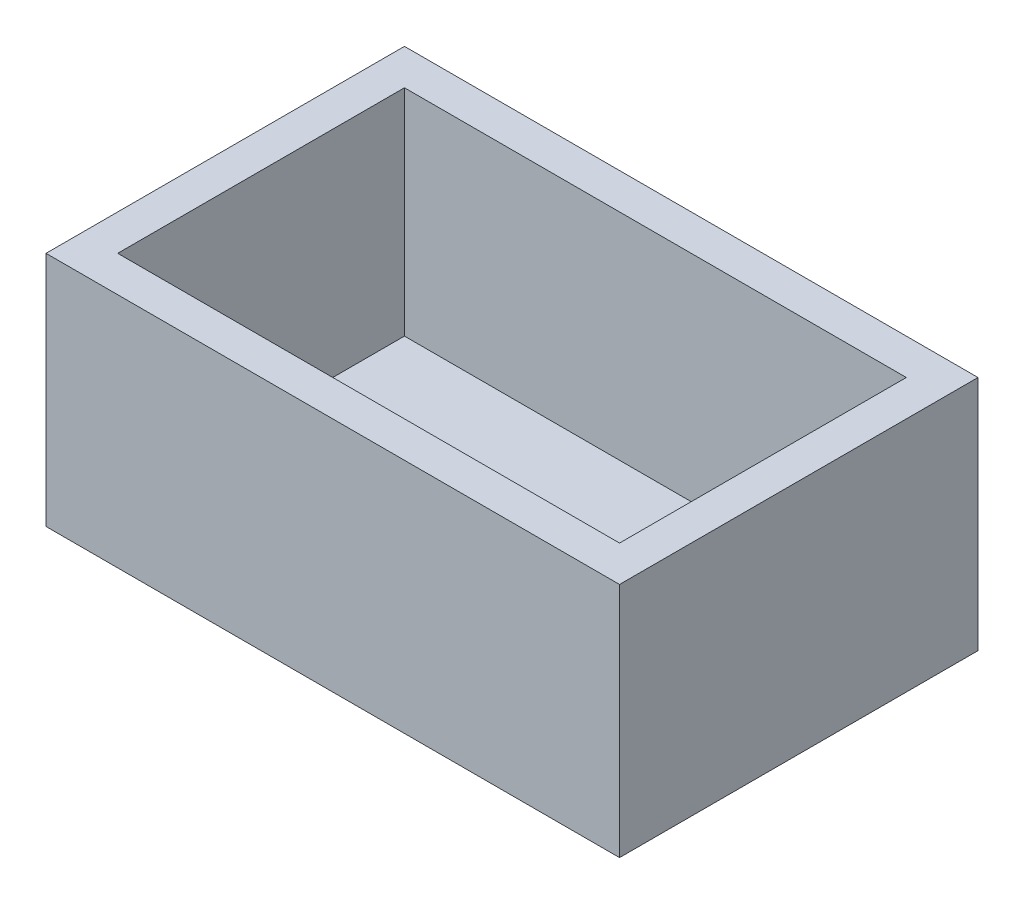
SolidWorks part; units mm, degrees
ref_plane "Front Plane" through (0, 0, 0) normal (0, 0, 1) x (1, 0, 0)
ref_plane "Top Plane" through (0, 0, 0) normal (0, 1, 0) x (1, 0, 0)
ref_plane "Right Plane" through (0, 0, 0) normal (1, 0, 0) x (0, 0, -1)
sketch "Sketch1" plane through (0, 0, 0) normal (0, 1, 0) x (1, 0, 0)
  line L1 (-40, 25) -> (40, 25)
  line L2 (-40, 25) -> (-40, -25)
  line L3 (-40, -25) -> (40, -25)
  line L4 (40, 25) -> (40, -25)
  line L5 (-40, 25) -> (40, -25) construction
  line L6 (-40, -25) -> (40, 25) construction
  point P0 (0, 0)
  dimension "D1" = 50
  dimension "D2" = 80
extrude "Boss-Extrude1" add sketch "Sketch1" along normal blind 3
sketch "Sketch2" plane through (0, 3, 0) normal (0, 1, 0) x (1, 0, 0)
  line L0 (-35, 20) -> (-35, -20)
  line L1 (-35, -20) -> (35, -20)
  line L2 (35, -20) -> (35, 20)
  line L3 (35, 20) -> (-35, 20)
  line L4 (40, -25) -> (40, 25)
  line L5 (40, 25) -> (-40, 25)
  line L6 (-40, 25) -> (-40, -25)
  line L7 (-40, -25) -> (40, -25)
  line L8 (40, -25) -> (40, 25)
  line L9 (40, 25) -> (-40, 25)
  line L10 (-40, 25) -> (-40, -25)
  line L11 (-40, -25) -> (40, -25)
  dimension "D1" = 0
  dimension "D2" = 5
extrude "Boss-Extrude2" add sketch "Sketch2" along normal blind 30
